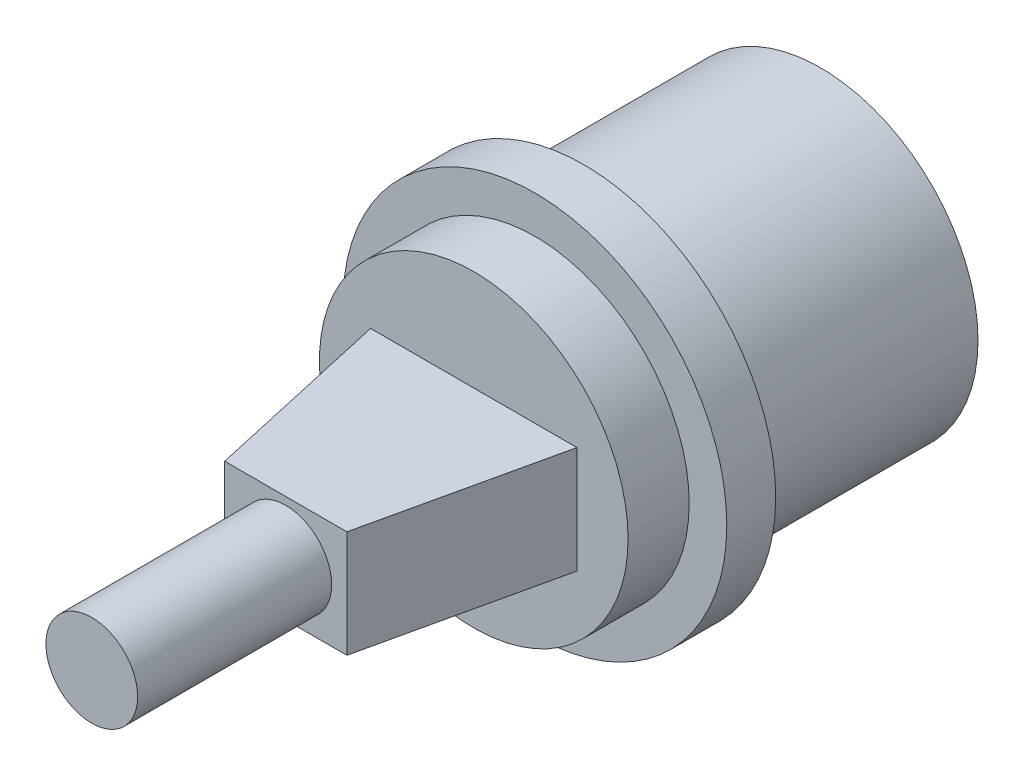
SolidWorks part; units mm, degrees
ref_plane "Front Plane" through (0, 0, 0) normal (0, 0, 1) x (1, 0, 0)
ref_plane "Top Plane" through (0, 0, 0) normal (0, 1, 0) x (1, 0, 0)
ref_plane "Right Plane" through (0, 0, 0) normal (1, 0, 0) x (0, 0, -1)
sketch "Sketch1" plane through (0, 0, 0) normal (1, 0, 0) x (0, 0, -1)
  line L0 (-32.2, 0) -> (15.5, 0)
  line L1 (15.5, 0) -> (15.5, 10.3)
  line L2 (15.5, 10.3) -> (0, 10.3)
  line L3 (0, 10.3) -> (0, 12.56)
  line L4 (0, 12.56) -> (-3.2, 12.56)
  line L5 (-3.2, 12.56) -> (-3.2, 10.1)
  line L6 (-3.2, 10.1) -> (-7.2, 10.1)
  line L7 (-7.2, 10.1) -> (-7.2, 3)
  line L8 (-7.2, 3) -> (-32.2, 3)
  line L9 (-32.2, 3) -> (-32.2, 0)
  line L10 (15.5, 0) -> (34.1006, 0) construction
  dimension "D1" = 20.6
  dimension "D2" = 25.12
  dimension "D3" = 15.5
  dimension "D4" = 3.2
  dimension "D5" = 4
  dimension "D6" = 20.2
  dimension "D7" = 6
  dimension "D8" = 25
revolve "Revolve1" add sketch "Sketch1" angle 360 about L10
sketch "Sketch2" plane through (0, 0, 0) normal (0, 1, 0) x (1, 0, 0)
  line L0 (-6.75, -7.2) -> (6.75, -7.2)
  line L1 (6.75, -7.2) -> (4, -19.5)
  line L2 (4, -19.5) -> (-4, -19.5)
  line L3 (-4, -19.5) -> (-6.75, -7.2)
  line L4 (0, -7.2) -> (0, 0) construction
  line L5 (-10.1, -7.2) -> (10.1, -7.2) construction
  dimension "D1" = 8
  dimension "D2" = 13.5
  dimension "D3" = 12.3
extrude "Boss-Extrude1" add sketch "Sketch2" along normal mid plane 7
sketch "Sketch3" plane through (0, 0, -15.5) normal (0, 0, -1) x (-1, 0, 0)
  line L1 (6.75, -3) -> (-6.75, -3)
  line L2 (6.75, -3) -> (6.75, 3)
  line L3 (6.75, 3) -> (-6.75, 3)
  line L4 (-6.75, -3) -> (-6.75, 3)
  line L5 (6.75, -3) -> (-6.75, 3) construction
  line L6 (6.75, 3) -> (-6.75, -3) construction
  point P0 (0, 0)
  dimension "D1" = 6
  dimension "D2" = 13.5
extrude "Cut-Extrude1" cut sketch "Sketch3" against normal blind 10
sketch "Sketch4" plane through (0, 0, -15.5) normal (0, 0, -1) x (-1, 0, 0)
  line L0 (8.6, 5.6683) -> (8.6, -5.6683)
  circle A0 centre (0, 0) radius 10.3 construction
  arc A1 (8.6, -5.6683) -> (8.6, 5.6683) centre (0, 0) ccw
  dimension "D1" = 18.9
extrude "Cut-Extrude2" cut sketch "Sketch4" against normal up to surface (15.5 mm away) up to face at (12.56, 0, 0)
